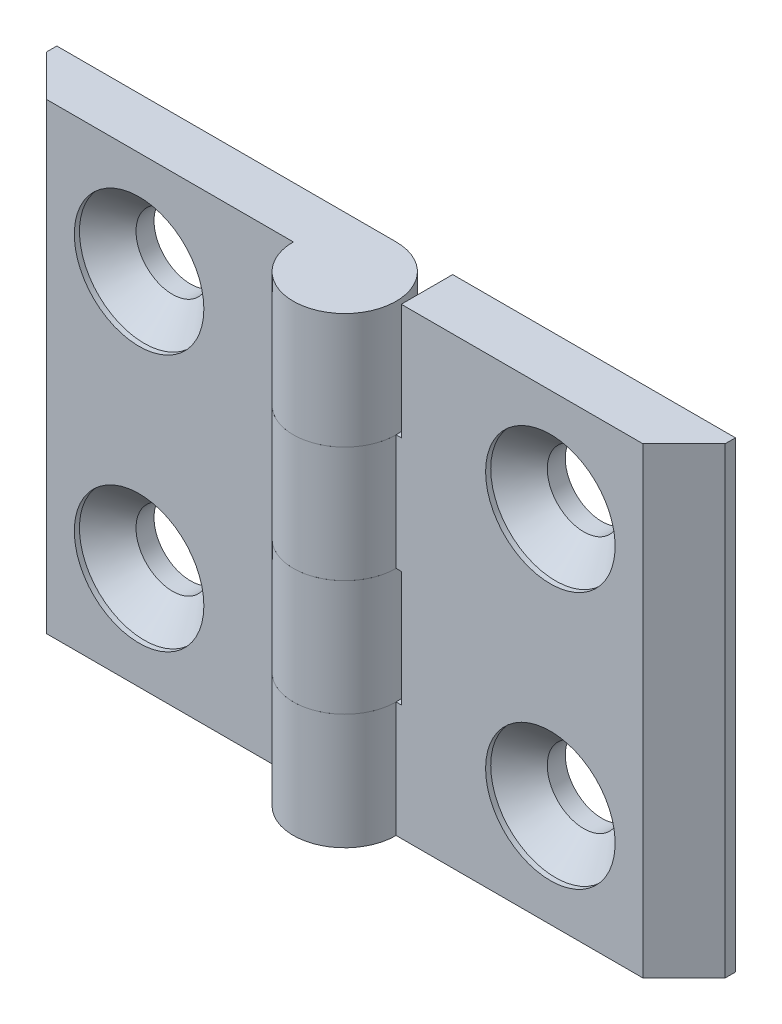
SolidWorks part; units mm, degrees
material "Алюминиевый сплав"
ref_plane "Спереди" through (0, 0, 0) normal (0, 0, 1) x (1, 0, 0)
ref_plane "Сверху" through (0, 0, 0) normal (0, 1, 0) x (1, 0, 0)
ref_plane "Справа" through (0, 0, 0) normal (1, 0, 0) x (0, 0, -1)
sketch "Эскиз1" plane through (0, 0, 0) normal (0, 1, 0) x (1, 0, 0)
  line L0 (0, 5) -> (-33, 5)
  line L1 (-33, 5) -> (-33, 4)
  line L2 (-33, 4) -> (-29, 0)
  line L3 (-29, 0) -> (-5, 0)
  line L4 (0, 0) -> (0, 10.5526) construction
  arc A0 (-5, 0) -> (0, 5) centre (0, 0) ccw
  dimension "D1" = 66
  dimension "D2" = 5
  dimension "D3" = 1
  dimension "D4" = 45
extrude "Бобышка-Вытянуть1" add sketch "Эскиз1" along normal mid plane 45
sketch "Эскиз3" plane through (0, 0, 0) normal (0, 0, 1) x (1, 0, 0)
  line L0 (5, -22.5) -> (5, 22.5) construction
  line L1 (-5.5, 11.25) -> (5, 11.25)
  line L2 (-5.5, 11.25) -> (-5.5, 0)
  line L3 (-5.5, 0) -> (5, 0)
  line L4 (5, 11.25) -> (5, 0)
  line L5 (5, 0) -> (5, -11.25) construction
  line L6 (5, -22.5) -> (-5.5, -22.5)
  line L7 (5, -22.5) -> (5, -11.25)
  line L8 (5, -11.25) -> (-5.5, -11.25)
  line L9 (-5.5, -22.5) -> (-5.5, -11.25)
  line L10 (5, 11.25) -> (5, 22.5) construction
  line L11 (-5, 22.5) -> (-5, -22.5) construction
  dimension "D1" = 0.5
extrude "Вырез-Вытянуть1" cut sketch "Эскиз3" against normal through all and the other way through all
hole_wizard "Зенковка для винта с полупотайной головкой M61" positions "Эскиз4" profile "Эскиз6" countersink size "M6" standard "ISO" end condition through all
sketch "Эскиз4" plane through (0, 0, 0) normal (0, 0, 1) x (1, 0, 0)
  line L0 (-20, 12.5) -> (-20, -12.5)
  line L2 (0, 0) -> (0, 18.9001) construction
  line L3 (5, 0) -> (-5, 0) construction
  point P0 (-20, 12.5)
  point P2 (-20, -12.5)
  point P9 (-20, 0)
  dimension "D1" = 25
  dimension "D2" = 40
sketch "Эскиз6" plane through (-20, 12.5, 0) normal (1, 0, 0) x (0, -1, 0)
  line L0 (0, 0) -> (0, 5)
  line L1 (0, 5) -> (3.55, 5)
  line L2 (3.55, 5) -> (3.55, 3.25)
  line L3 (3.55, 3.25) -> (6.3, 0.5)
  line L4 (6.3, 0.5) -> (6.3, 0)
  line L6 (6.3, 0) -> (0, 0)
  line L7 (-3.55, 3.25) -> (-6.3, 0.5) construction
  line L11 (0, -6.35) -> (0, 107.95) construction
  dimension "Диаметр сквозного отверстия" = 7.1
  dimension "Глубина сквозного отверстия" = 5
  dimension "Диаметр зенковки" = 12.6
  dimension "Угол зенковки" = 90
  dimension "Утопленность" = 0.5
sketch "Угол раскрытия" plane through (0, 0, 0) normal (0, 1, 0) x (1, 0, 0)
  line L0 (0, 0) -> (0, -10)
  line L7 (0, 5) -> (-33, 5) construction
  point P3 (-11.2006, -8.7746)
  point P8 (-7.4924, -9.3736)
  point P9 (0, 0)
  point P10 (-11.8016, -2.1731)
  dimension "D1" = 10
  dimension "D2" = 90
pattern_circular "Круговой массив1" count 2 over 360 about axis through (0, 0, 0) along (0, 0, 1) of bodies 106
